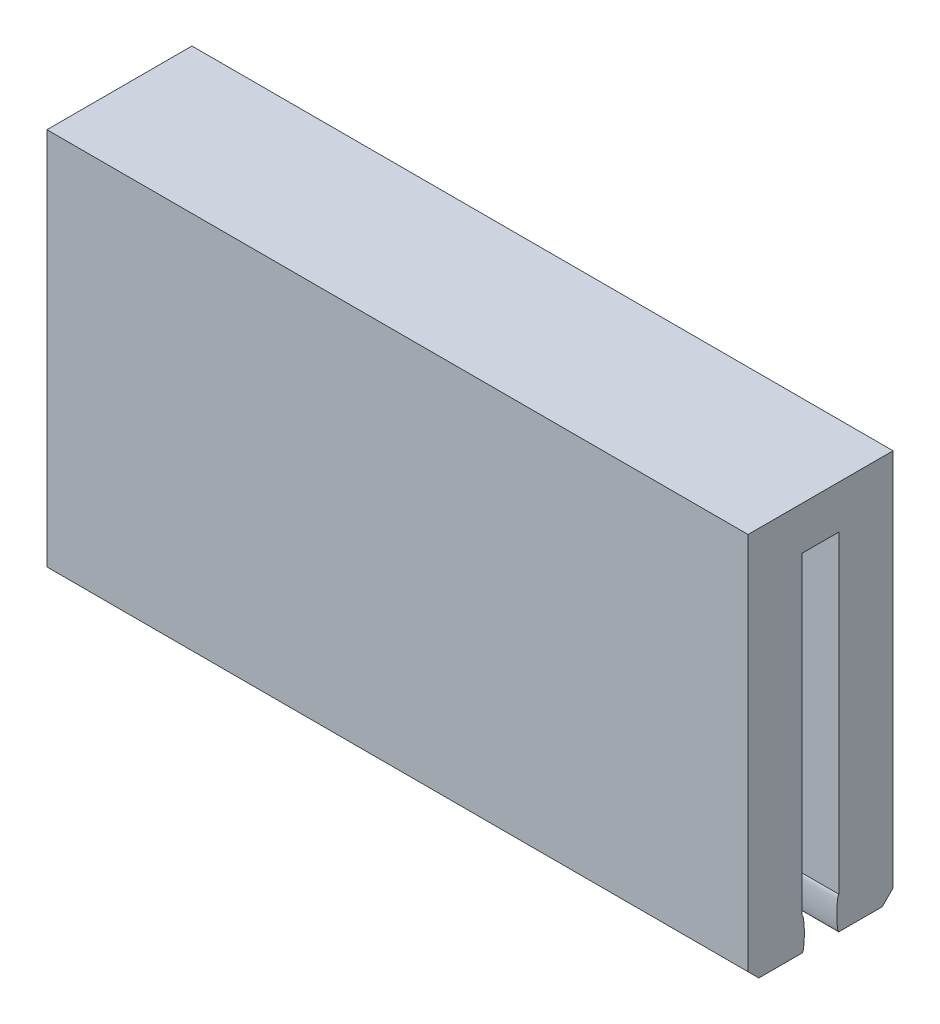
SolidWorks part; units mm, degrees
ref_plane "Front Plane" through (0, 0, 0) normal (0, 0, 1) x (1, 0, 0)
ref_plane "Top Plane" through (0, 0, 0) normal (0, 1, 0) x (1, 0, 0)
ref_plane "Right Plane" through (0, 0, 0) normal (1, 0, 0) x (0, 0, -1)
sketch "Sketch1" plane through (0, 0, 0) normal (0, 1, 0) x (1, 0, 0)
  line L0 (-14.2, 0.85) -> (-16.2, 0.85)
  line L1 (-16.2, 3.35) -> (16.2, 3.35)
  line L3 (-16.2, -3.35) -> (16.2, -3.35)
  line L5 (-16.2, 3.35) -> (16.2, -3.35) construction
  line L6 (-16.2, -3.35) -> (16.2, 3.35) construction
  line L7 (-14.2, -0.85) -> (-16.2, -0.85)
  line L8 (14.2, 0.85) -> (16.2, 0.85)
  line L9 (14.2, -0.85) -> (16.2, -0.85)
  line L10 (-14.2, 1.35) -> (14.2, 1.35)
  line L12 (14.2, -1.35) -> (-14.2, -1.35)
  line L14 (-14.2, 1.35) -> (-14.2, 0.85)
  line L15 (-14.2, -0.85) -> (-14.2, -1.35)
  line L16 (14.2, 1.35) -> (14.2, 0.85)
  line L17 (14.2, -0.85) -> (14.2, -1.35)
  line L18 (-16.2, 3.35) -> (-16.2, 0.85)
  line L19 (-16.2, -3.35) -> (-16.2, -0.85)
  line L20 (16.2, 3.35) -> (16.2, 0.85)
  line L21 (16.2, -0.85) -> (16.2, -3.35)
  point P1 (0, 0)
  dimension "D1" = 32.4
  dimension "D2" = 6.7
  dimension "D3" = 2
  dimension "D4" = 2
  dimension "D5" = 0.5
  dimension "D6" = 0.5
  dimension "D7" = 2
  dimension "D8" = 2
extrude "Boss-Extrude1" add sketch "Sketch1" along normal blind 16
sketch "Sketch2" plane through (0, 16, 0) normal (0, 1, 0) x (1, 0, 0)
  line L1 (-16.2, -3.35) -> (16.2, -3.35)
  line L2 (-16.2, -3.35) -> (-16.2, 3.35)
  line L3 (-16.2, 3.35) -> (16.2, 3.35)
  line L4 (16.2, -3.35) -> (16.2, 3.35)
  line L5 (-16.2, -3.35) -> (16.2, 3.35) construction
  line L6 (-16.2, 3.35) -> (16.2, -3.35) construction
  point P0 (0, 0)
extrude "Boss-Extrude2" add sketch "Sketch2" along normal blind 2
chamfer "Chamfer1" distance 0.5 angle 83 2 edges at (0, 0, -1.35) (0, 0, 1.35)
chamfer "Chamfer4" distance 0.5 angle 45 2 edges at (0, 0, 3.35) (0, 0, -3.35)
sketch "Sketch4" plane through (16.2, 0, 0) normal (1, 0, 0) x (0, 0, -1)
  line L0 (3.35, 1.5) -> (-3.35, 1.5) construction
  line L1 (3.35, 18) -> (3.35, 0.5) construction
  line L2 (-3.35, 18) -> (-3.35, 0.5) construction
  line L3 (-2.85, 0) -> (-0.85, 0) construction
  line L4 (-0.85, 16) -> (-0.85, 0) construction
  line L5 (0.85, 16) -> (0.85, 0) construction
  ellipse E0 centre (-0.85, 0.75) end of major axis (-0.85, 1.5) minor radius 0.1
  ellipse E1 centre (0.85, 0.75) end of major axis (0.85, 1.5) minor radius 0.1
  dimension "D1" = 1.5
  dimension "D2" = 0.75
  dimension "D3" = 0.1
  dimension "D4" = 0.1
  dimension "D5" = 0.75
extrude "Boss-Extrude3" add sketch "Sketch4" against normal blind 2
sketch "Sketch5" plane through (-16.2, 0, 0) normal (-1, 0, 0) x (0, 0, 1)
  line L0 (-3.35, 1.5) -> (3.35, 1.5) construction
  line L1 (-3.35, 18) -> (-3.35, 0.5) construction
  line L2 (3.35, 18) -> (3.35, 0.5) construction
  line L3 (-2.85, 0) -> (-0.85, 0) construction
  line L4 (-0.85, 16) -> (-0.85, 0) construction
  line L5 (0.85, 16) -> (0.85, 0) construction
  ellipse E0 centre (-0.85, 0.75) end of major axis (-0.85, 0) minor radius 0.1
  ellipse E1 centre (0.85, 0.75) end of major axis (0.85, 0) minor radius 0.1
  dimension "D1" = 1.5
  dimension "D2" = 0.75
  dimension "D3" = 0.75
  dimension "D4" = 0.1
  dimension "D5" = 0.1
extrude "Boss-Extrude4" add sketch "Sketch5" against normal blind 2
